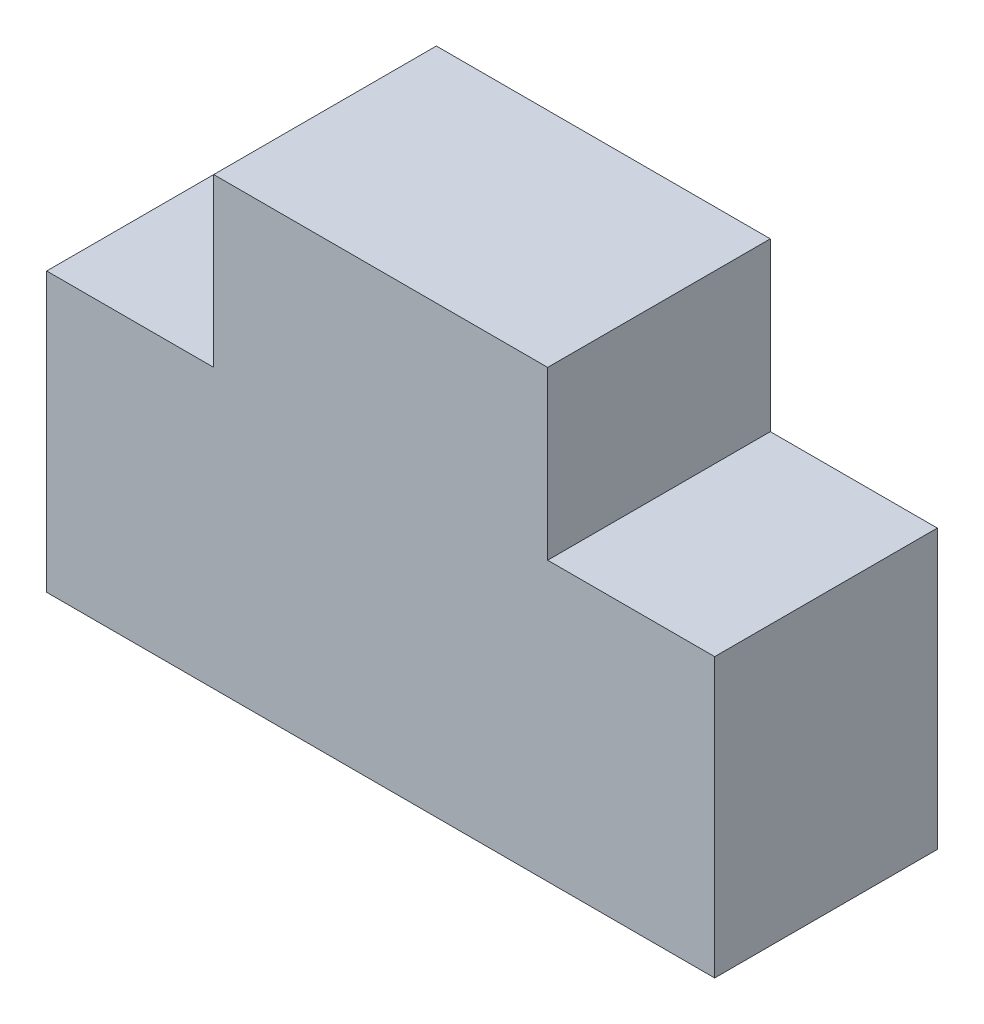
SolidWorks part; units mm, degrees
material "ABS"
ref_plane "Front Plane" through (0, 0, 0) normal (0, 0, 1) x (1, 0, 0)
ref_plane "Top Plane" through (0, 0, 0) normal (0, 1, 0) x (1, 0, 0)
ref_plane "Right Plane" through (0, 0, 0) normal (1, 0, 0) x (0, 0, -1)
sketch "Sketch1" plane through (0, 0, 0) normal (0, 0, 1) x (1, 0, 0)
  line L1 (-38.1, 25.4) -> (38.1, 25.4)
  line L2 (-38.1, 25.4) -> (-38.1, -25.4)
  line L3 (-38.1, -25.4) -> (38.1, -25.4)
  line L4 (38.1, 25.4) -> (38.1, -25.4)
  dimension "D1" = 38.1
  dimension "D2" = 38.1
  dimension "D3" = 25.4
  dimension "D4" = 25.4
extrude "Boss-Extrude1" add sketch "Sketch1" along normal mid plane 25.4
sketch "Sketch2" plane through (0, 0, 12.7) normal (0, 0, 1) x (1, 0, 0)
  line L1 (-38.1, 25.4) -> (-19.05, 25.4)
  line L2 (-38.1, 25.4) -> (-38.1, 6.35)
  line L3 (-38.1, 6.35) -> (-19.05, 6.35)
  line L4 (-19.05, 25.4) -> (-19.05, 6.35)
  dimension "D1" = 19.05
  dimension "D2" = 19.05
extrude "Cut-Extrude1" cut sketch "Sketch2" against normal through all
mirror "Mirror1" about plane through (0, 0, 0) normal (1, 0, 0) of "Cut-Extrude1"
